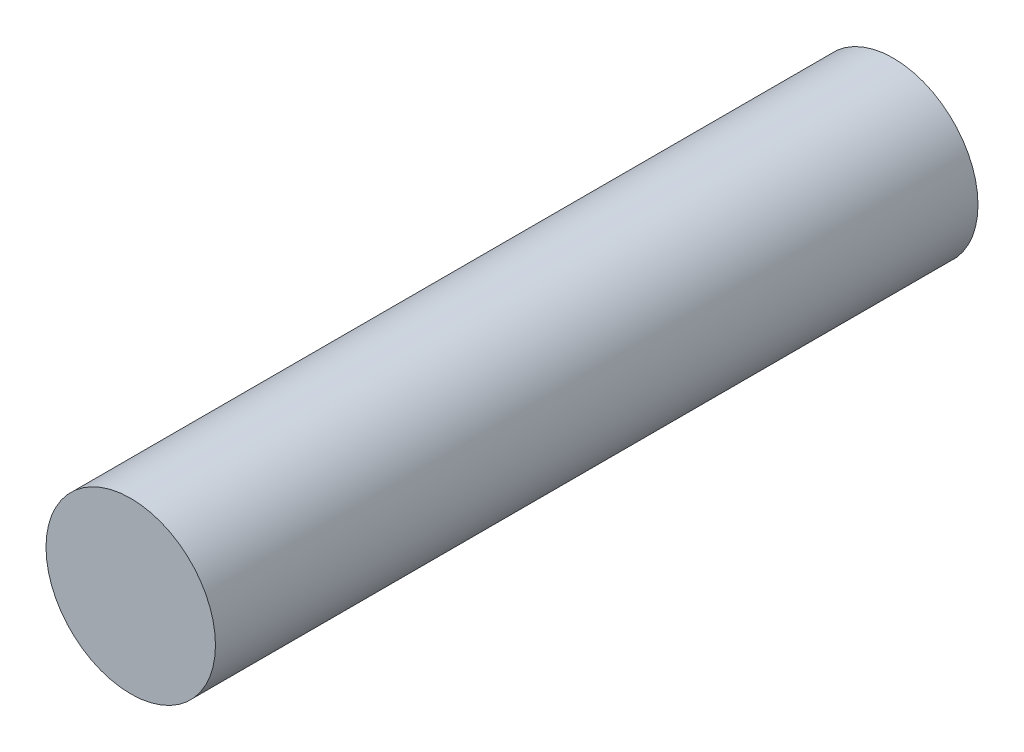
SolidWorks part; units mm, degrees
ref_plane "Alzado" through (0, 0, 0) normal (0, 0, 1) x (1, 0, 0)
ref_plane "Planta" through (0, 0, 0) normal (0, 1, 0) x (1, 0, 0)
ref_plane "Vista lateral" through (0, 0, 0) normal (1, 0, 0) x (0, 0, -1)
sketch "Croquis1" plane through (0, 0, 0) normal (0, 0, 1) x (1, 0, 0)
  circle A0 centre (0, 0) radius 2
  dimension "D1" = 4
extrude "Saliente-Extruir1" add sketch "Croquis1" along normal blind 18
